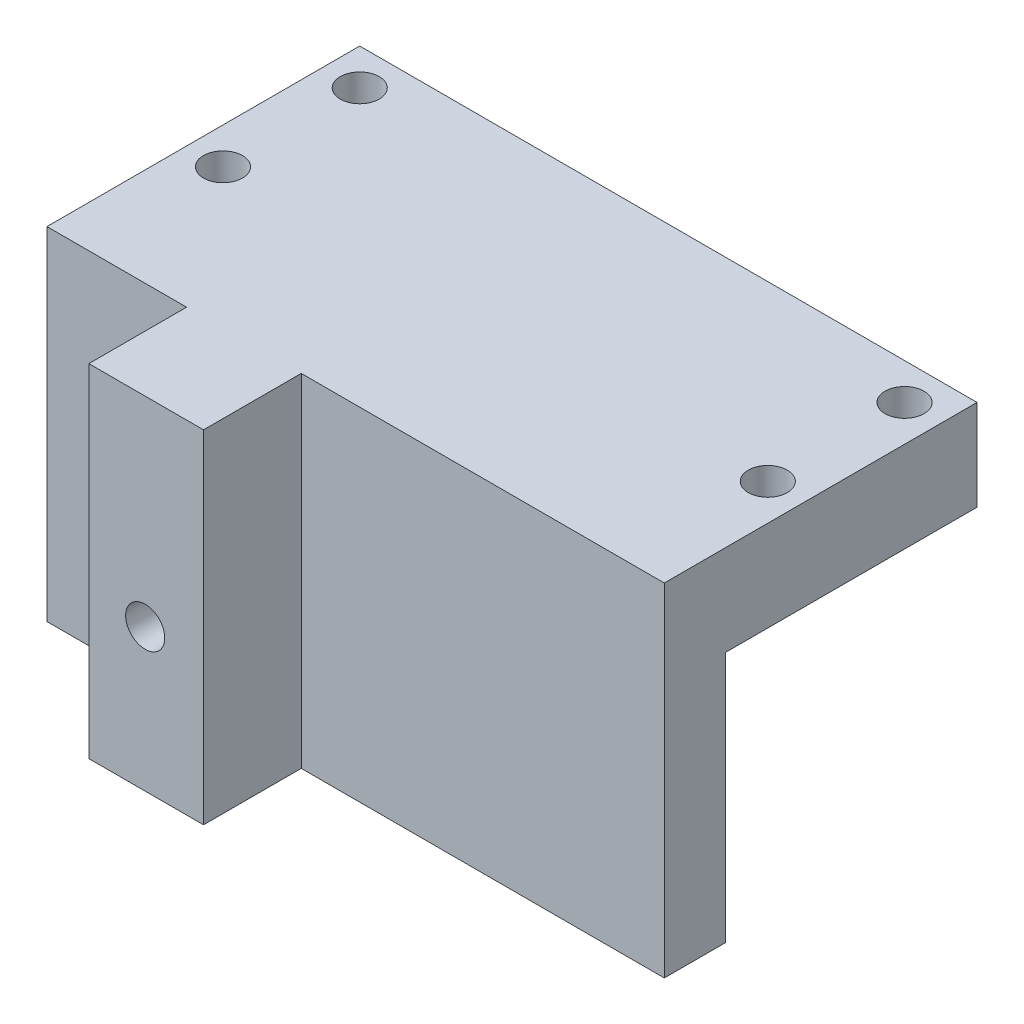
SolidWorks part; units mm, degrees
ref_plane "Front Plane" through (0, 0, 0) normal (0, 0, 1) x (1, 0, 0)
ref_plane "Top Plane" through (0, 0, 0) normal (0, 1, 0) x (1, 0, 0)
ref_plane "Right Plane" through (0, 0, 0) normal (1, 0, 0) x (0, 0, -1)
sketch "Sketch1" plane through (0, 0, 0) normal (0, 1, 0) x (1, 0, 0)
  line L1 (0, 0) -> (56.15, 0)
  line L2 (0, 0) -> (0, 25.4)
  line L3 (0, 25.4) -> (56.15, 25.4)
  line L4 (56.15, 0) -> (56.15, 25.4)
  dimension "D1" = 56.15
  dimension "D2" = 25.4
extrude "Boss-Extrude1" add sketch "Sketch1" against normal blind 2.54
sketch "Sketch2" plane through (0, 0, 0) normal (0, 0, 1) x (1, 0, 0)
  line L1 (0, 0) -> (56.15, 0)
  line L2 (0, 0) -> (0, -25.4)
  line L3 (0, -25.4) -> (56.15, -25.4)
  line L4 (56.15, 0) -> (56.15, -25.4)
  dimension "D1" = 25.4
extrude "Boss-Extrude2" add sketch "Sketch2" against normal blind 2.54
ref_plane "Plane3" through (0, -2.54, 0) normal (0, -1, 0) x (-1, 0, 0)
sketch "Sketch11" plane through (0, 0, 0) normal (0, 1, 0) x (1, 0, 0)
  line L1 (56.15, 0) -> (0, 0)
  line L2 (56.15, 0) -> (56.15, 25.4)
  line L3 (56.15, 25.4) -> (0, 25.4)
  line L4 (0, 0) -> (0, 25.4)
extrude "Boss-Extrude3" add sketch "Sketch11" along normal blind 5.715
sketch "Sketch6" plane through (0, -2.54, 0) normal (0, -1, 0) x (1, 0, 0)
  line L0 (51.078, -22.102) -> (54.626, -22.102) construction
  line L5 (51.078, -20.328) -> (54.626, -20.328)
  line L6 (51.078, -20.328) -> (51.078, -23.876)
  line L7 (51.078, -23.876) -> (54.626, -23.876)
  line L8 (54.626, -20.328) -> (54.626, -23.876)
  line L9 (52.852, -22.102) -> (52.852, -23.876) construction
  line L10 (52.852, -22.102) -> (52.852, -20.328) construction
  line L11 (56.15, -25.4) -> (54.626, -25.4)
  line L12 (52.852, -20.328) -> (52.852, -11.438) construction
  line L13 (52.852, -11.438) -> (52.852, -9.664) construction
  line L14 (56.15, -25.4) -> (56.15, -23.876)
  line L15 (56.15, -23.876) -> (54.626, -23.876)
  line L16 (54.626, -25.4) -> (54.626, -23.876)
  line L17 (28.075, -25.4) -> (28.075, -2.54) construction
  line L18 (56.15, -25.4) -> (0, -25.4) construction
  line L19 (56.15, -2.54) -> (0, -2.54) construction
  circle A0 centre (52.852, -22.102) radius 1.774
  circle A2 centre (52.852, -9.664) radius 1.774
  circle A3 centre (3.298, -22.102) radius 1.774
  circle A4 centre (3.298, -9.664) radius 1.774
  dimension "D1" = 8.89
  dimension "D3" = 3.548
  dimension "D4" = 3.548
  dimension "D5" = 1.524
  dimension "D6" = 1.524
extrude "Cut-Extrude3" cut sketch "Sketch6" against normal through all contours A0 | A2 | A4 | A3
sketch "Sketch8" plane through (0, -2.54, 0) normal (0, -1, 0) x (1, 0, 0)
  line L0 (56.15, -25.4) -> (0, -25.4) construction
  line L1 (28.075, -25.4) -> (28.075, 0) construction
ref_plane "Plane4" through (56.15, -2.54, -25.4) normal (0, 0, -1) x (-1, 0, 0)
sketch "Sketch13" plane through (0, 0, 0) normal (0, 0, 1) x (1, 0, 0)
  line L1 (56.15, -25.4) -> (0, -25.4)
  line L2 (56.15, -25.4) -> (56.15, 5.715)
  line L3 (56.15, 5.715) -> (0, 5.715)
  line L4 (0, -25.4) -> (0, 5.715)
extrude "Boss-Extrude4" add sketch "Sketch13" along normal offset from surface (11.938 mm away) 1.016
sketch "Sketch14" plane through (0, -25.4, 0) normal (0, -1, 0) x (1, 0, 0)
  line L0 (28.075, -2.54) -> (28.075, 11.938) construction
  line L1 (0, -2.54) -> (56.15, -2.54) construction
  line L2 (0, 11.938) -> (56.15, 11.938) construction
  line L3 (0, 3.048) -> (12.7, 3.048)
  line L4 (56.15, 11.938) -> (23.13, 11.938)
  line L5 (56.15, 11.938) -> (56.15, 3.048)
  line L6 (56.15, 3.048) -> (23.13, 3.048)
  line L7 (23.13, 11.938) -> (23.13, 3.048)
  line L8 (12.7, 11.938) -> (12.7, 3.048)
  line L9 (0, 11.938) -> (12.7, 11.938)
  line L10 (0, 11.938) -> (0, 3.048)
  point P15 (43.45, 3.048)
  dimension "D1" = 8.89
  dimension "D2" = 33.02
extrude "Cut-Extrude4" cut sketch "Sketch14" against normal through all
sketch "Sketch17" plane through (0, 0, -2.54) normal (0, 0, -1) x (-1, 0, 0)
  line L0 (0, -25.4) -> (-12.7, -25.4) construction
  line L1 (0, -25.4) -> (-56.15, -25.4) construction
  line L2 (0, -25.4) -> (-12.7, -25.4) construction
  line L3 (-56.15, -25.4) -> (-23.13, -25.4) construction
  line L4 (-23.13, -25.4) -> (-56.15, -25.4) construction
  line L5 (-56.15, -2.54) -> (0, -2.54) construction
  line L6 (-12.7, -25.4) -> (-23.13, -25.4)
  line L7 (-12.7, -25.4) -> (-12.7, -2.54)
  line L8 (-12.7, -2.54) -> (-23.13, -2.54)
  line L9 (-23.13, -25.4) -> (-23.13, -2.54)
extrude "Boss-Extrude5" add sketch "Sketch17" along normal blind 14.097
sketch "Sketch15" plane through (0, 0, 11.938) normal (0, 0, 1) x (1, 0, 0)
  line L0 (23.13, -12.45) -> (18.05, -12.45) construction
  line L1 (23.13, 5.715) -> (23.13, -25.4) construction
  circle A0 centre (17.825, -12.45) radius 1.778
  point P7 (0, 0)
  dimension "D3" = 3.556
  dimension "D1" = 5.08
extrude "Cut-Extrude5" cut sketch "Sketch15" against normal through all
ref_plane "Plane5" through (23.13, -25.4, 11.938) normal (1, 0, 0) x (0, 0, -1)
